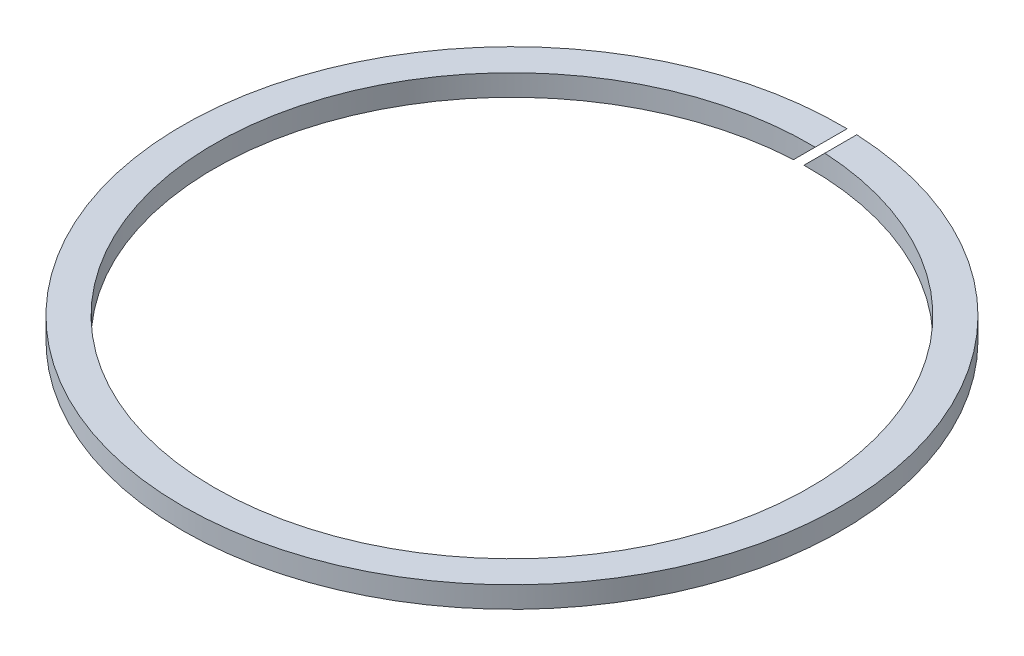
SolidWorks part; units mm, degrees
ref_plane "Front Plane" through (0, 0, 0) normal (0, 0, 1) x (1, 0, 0)
ref_plane "Top Plane" through (0, 0, 0) normal (0, 1, 0) x (1, 0, 0)
ref_plane "Right Plane" through (0, 0, 0) normal (1, 0, 0) x (0, 0, -1)
sketch "Sketch5" plane through (0, 0, 0) normal (0, 1, 0) x (1, 0, 0)
  circle A0 centre (0, 0) radius 42
  circle A1 centre (0, 0) radius 46.5
  dimension "D1" = 93
  dimension "D2" = 84
extrude "Boss-Extrude3" add sketch "Sketch5" along normal mid plane 3
sketch "Sketch6" plane through (0, 0, 0) normal (0, 0, 1) x (1, 0, 0)
  line L0 (-10.5688, -11.2759) -> (11.2759, 10.5688)
  line L1 (-10.5688, -11.2759) -> (-11.2759, -10.5688)
  line L2 (11.2759, 10.5688) -> (10.5688, 11.2759)
  line L3 (-11.2759, -10.5688) -> (10.5688, 11.2759)
  line L4 (-10.5688, -11.2759) -> (10.5688, 11.2759) construction
  line L5 (11.2759, 10.5688) -> (-11.2759, -10.5688) construction
  line L6 (46.5, 1.5) -> (-46.5, 1.5) construction
  point P1 (0, 0)
  point P3 (0, 0)
  dimension "D1" = 45
  dimension "D2" = 1
extrude "Cut-Extrude3" cut sketch "Sketch6" against normal blind 66 contours L0 L2 L3 L1
